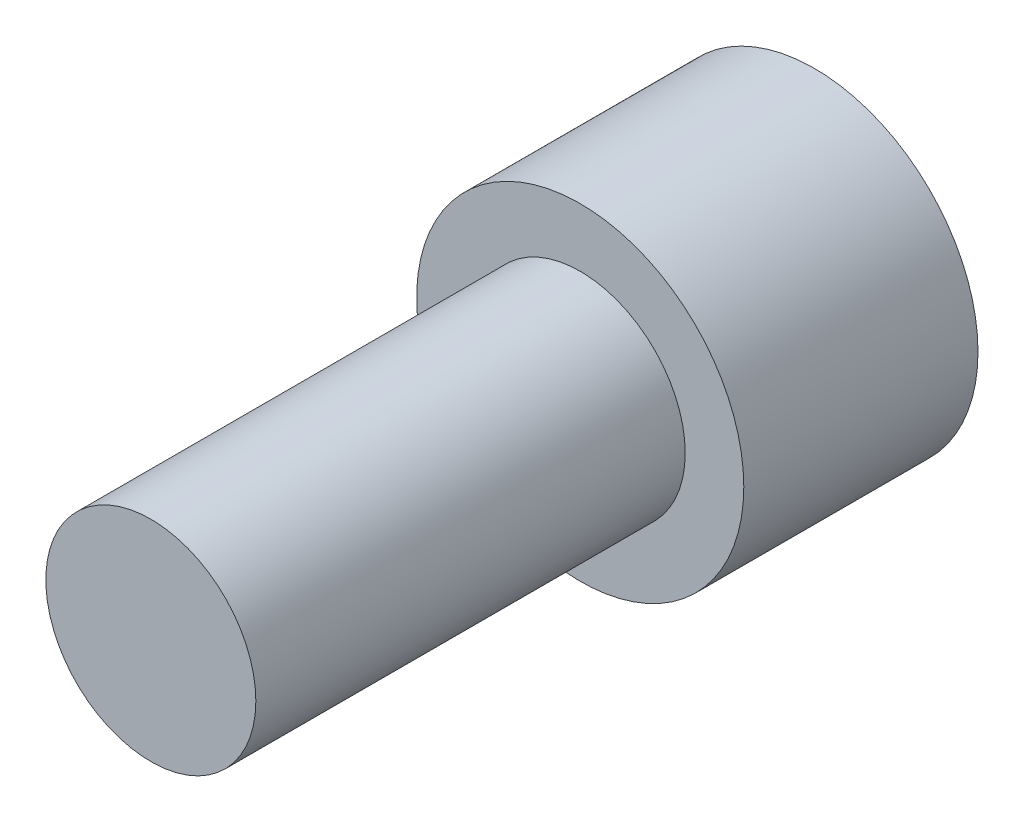
SolidWorks part; units mm, degrees
ref_plane "Front Plane" through (0, 0, 0) normal (0, 0, 1) x (1, 0, 0)
ref_plane "Top Plane" through (0, 0, 0) normal (0, 1, 0) x (1, 0, 0)
ref_plane "Right Plane" through (0, 0, 0) normal (1, 0, 0) x (0, 0, -1)
sketch "Sketch2" plane through (0, 0, 0) normal (0, 0, 1) x (1, 0, 0)
  circle A0 centre (0, 0) radius 4.191
  dimension "D1" = 8.382
extrude "Boss-Extrude1" add sketch "Sketch2" along normal blind 6
sketch "Sketch4" plane through (0, 0, 6) normal (0, 0, 1) x (1, 0, 0)
  circle A0 centre (0, 0) radius 2.69
  circle A1 centre (0, 0) radius 4.191 construction
  dimension "D1" = 5.38
extrude "Boss-Extrude2" add sketch "Sketch4" along normal blind 11
